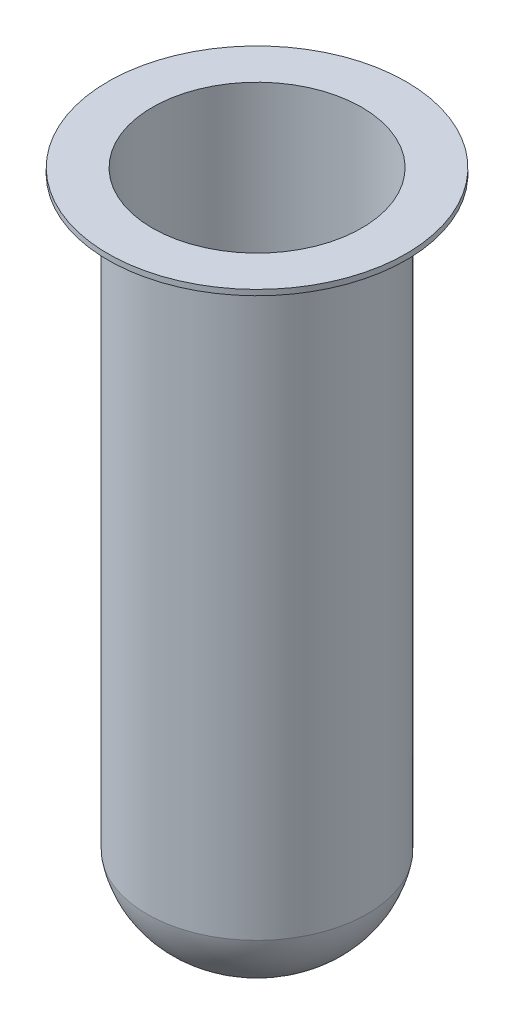
SolidWorks part; units mm, degrees
ref_plane "Front Plane" through (0, 0, 0) normal (0, 0, 1) x (1, 0, 0)
ref_plane "Top Plane" through (0, 0, 0) normal (0, 1, 0) x (1, 0, 0)
ref_plane "Right Plane" through (0, 0, 0) normal (1, 0, 0) x (0, 0, -1)
sketch "Sketch2" plane through (0, 0, 0) normal (0, 0, 1) x (1, 0, 0)
  line L0 (0, 0) -> (0, 120) construction
  line L2 (20, 120) -> (20, 13.6923)
  line L3 (20, 120) -> (27.0598, 120)
  line L4 (19, 121) -> (27.0598, 121)
  line L5 (19, 121) -> (19, 13.7865)
  line L6 (27.0598, 121) -> (27.0598, 120)
  line L7 (0.184, 0.9829) -> (0, 0.9297)
  line L8 (0, 0) -> (0, 0.9297)
  arc A0 (20, 13.6923) -> (0, 0) centre (3.1539, 16.8461) cw
  arc A1 (19, 13.7865) -> (0.184, 0.9829) centre (3.1539, 16.8461) cw
  dimension "D1" = 1
revolve "Revolve2" add sketch "Sketch2" angle 360 about L0
